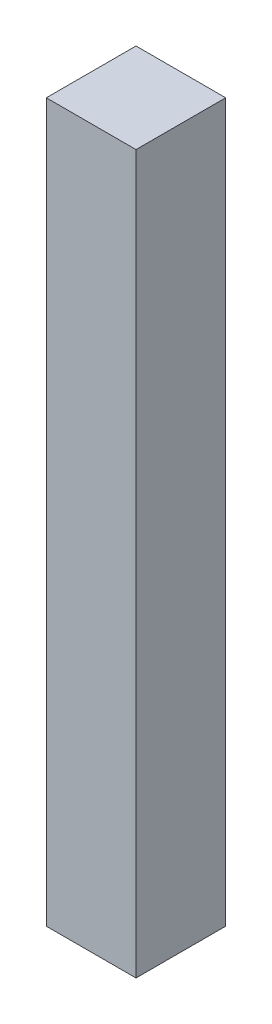
SolidWorks part; units mm, degrees
ref_plane "Front Plane" through (0, 0, 0) normal (0, 0, 1) x (1, 0, 0)
ref_plane "Top Plane" through (0, 0, 0) normal (0, 1, 0) x (1, 0, 0)
ref_plane "Right Plane" through (0, 0, 0) normal (1, 0, 0) x (0, 0, -1)
sketch "Sketch2" plane through (0, 0, 0) normal (0, 0, 1) x (1, 0, 0)
  line L1 (-1.5875, -12.7) -> (1.5875, -12.7)
  line L2 (-1.5875, -12.7) -> (-1.5875, 12.7)
  line L3 (-1.5875, 12.7) -> (1.5875, 12.7)
  line L4 (1.5875, -12.7) -> (1.5875, 12.7)
  line L5 (-1.5875, -12.7) -> (1.5875, 12.7) construction
  line L6 (-1.5875, 12.7) -> (1.5875, -12.7) construction
  point P0 (0, 0)
  dimension "D1" = 3.175
  dimension "D2" = 25.4
extrude "Boss-Extrude1" add sketch "Sketch2" along normal blind 3.175
equation "\"side thickness\"= 1 / 8in"
equation "\"extrude thickness\"= 1 / 8in"
equation "\"length\"= 1in"
equation "\"D1@Sketch2\"=\"side thickness\""
equation "\"D2@Sketch2\"=\"length\""
equation "\"D1@Boss-Extrude1\"=\"extrude thickness\""
